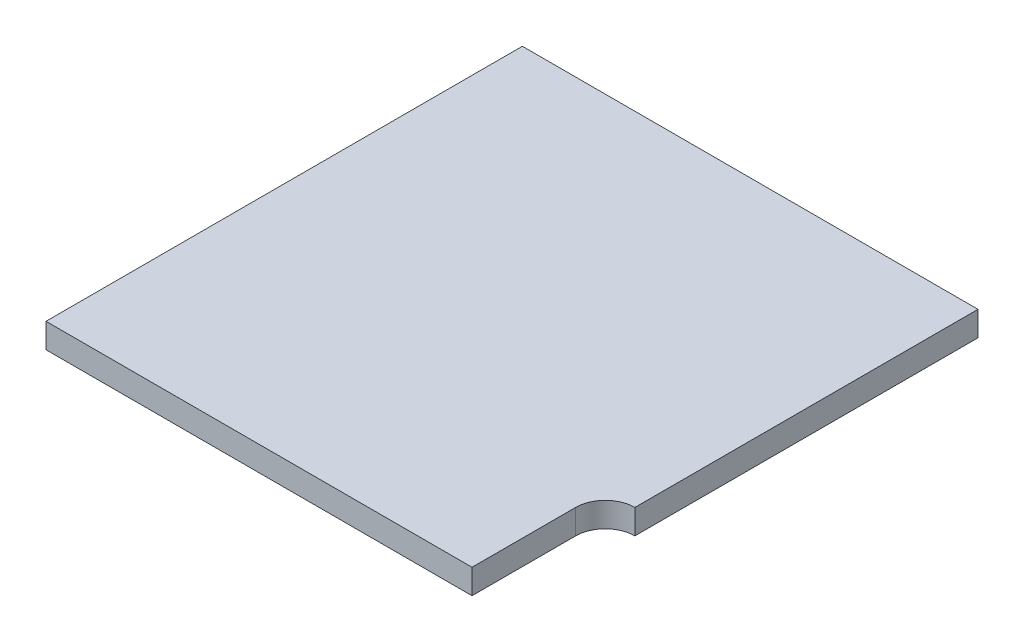
SolidWorks part; units mm, degrees
ref_plane "前视基准面" through (0, 0, 0) normal (0, 0, 1) x (1, 0, 0)
ref_plane "上视基准面" through (0, 0, 0) normal (0, 1, 0) x (1, 0, 0)
ref_plane "右视基准面" through (0, 0, 0) normal (1, 0, 0) x (0, 0, -1)
sketch "草图1" plane through (0, 0, 0) normal (0, 1, 0) x (1, 0, 0)
  line L1 (-9.23, -9.65) -> (9.23, -9.65)
  line L2 (-9.23, -9.65) -> (-9.23, 9.65)
  line L3 (-9.23, 9.65) -> (9.23, 9.65)
  line L4 (9.23, -9.65) -> (9.23, 9.65)
  line L5 (-9.23, -9.65) -> (9.23, 9.65) construction
  line L6 (-9.23, 9.65) -> (9.23, -9.65) construction
  point P0 (0, 0)
  dimension "D1" = 18.46
  dimension "D2" = 19.3
extrude "凸台-拉伸1" add sketch "草图1" along normal blind 1
ref_plane "基准面1" through (0, 0, 0) normal (1, 0, 0) x (0, 0, -1)
ref_plane "基准面2" through (0, 0, 0) normal (0, 0, -1) x (-1, 0, 0)
sketch "草图2" plane through (0, 1, 0) normal (0, 1, 0) x (1, 0, 0)
  line L0 (9.23, -9.65) -> (9.23, 9.65) construction
  line L1 (9.23, -9.65) -> (8.03, -9.65)
  line L2 (9.23, -9.65) -> (9.23, -4.25)
  line L4 (8.03, -9.65) -> (8.03, -5.45)
  arc A0 (8.03, -5.45) -> (9.23, -4.25) centre (9.23, -5.45) cw
  dimension "D1" = 4.2
  dimension "D2" = 1.2
extrude "切除-拉伸1" cut sketch "草图2" against normal through all
